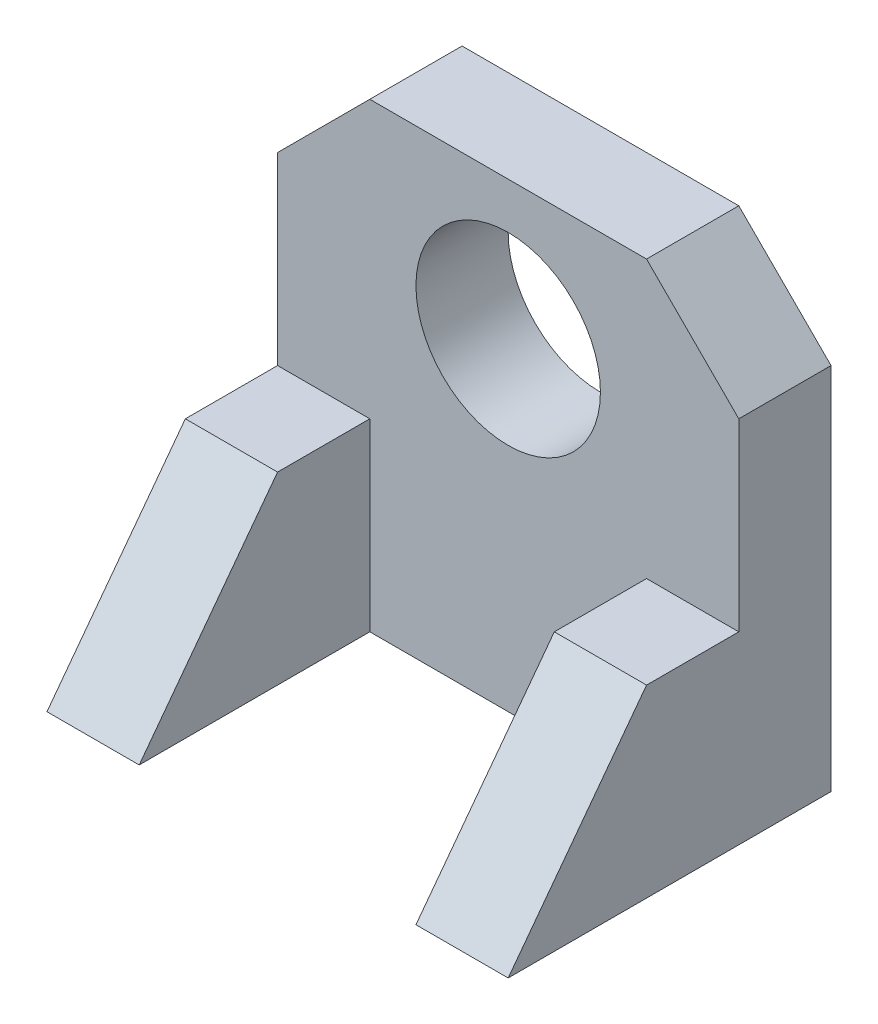
SolidWorks part; units mm, degrees
ref_plane "Front Plane" through (0, 0, 0) normal (0, 0, 1) x (1, 0, 0)
ref_plane "Top Plane" through (0, 0, 0) normal (0, 1, 0) x (1, 0, 0)
ref_plane "Right Plane" through (0, 0, 0) normal (1, 0, 0) x (0, 0, -1)
sketch "Sketch1" plane through (0, 0, 0) normal (0, 0, 1) x (1, 0, 0)
  line L1 (-15.7517, 35.0566) -> (14.2483, 35.0566)
  line L2 (-25.7517, 25.0566) -> (-25.7517, -14.9434)
  line L3 (-25.7517, -14.9434) -> (24.2483, -14.9434)
  line L4 (24.2483, 25.0566) -> (24.2483, -14.9434)
  line L5 (-15.7517, 35.0566) -> (-25.7517, 25.0566)
  line L8 (14.2483, 35.0566) -> (24.2483, 25.0566)
  dimension "D1" = 50
extrude "Boss-Extrude1" add sketch "Sketch1" against normal blind 10
sketch "Sketch2" plane through (0, 0, 0) normal (0, 0, 1) x (1, 0, 0)
  circle A0 centre (-0.7517, 20.0566) radius 10
extrude "Cut-Extrude1" cut sketch "Sketch2" against normal blind 10
sketch "Sketch3" plane through (24.2483, 0, 0) normal (1, 0, 0) x (0, 0, -1)
  line L0 (0, -14.9434) -> (-25, -14.9434)
  line L2 (0, -14.9434) -> (0, 25.0566) construction
  line L3 (0, 5.0566) -> (0, -14.9434)
  line L4 (0, 5.0566) -> (-10, 5.0566)
  line L5 (-10, 5.0566) -> (-25, -14.9434)
  dimension "D1" = 25
  dimension "D2" = 10
  dimension "D3" = 20
extrude "Boss-Extrude2" add sketch "Sketch3" against normal blind 10
sketch "Sketch4" plane through (-25.7517, 0, 0) normal (-1, 0, 0) x (0, 0, 1)
  line L0 (0, -14.9434) -> (25, -14.9434)
  line L1 (25, -14.9434) -> (10, 5.0566)
  line L2 (10, 5.0566) -> (0, 5.0566)
  line L3 (0, 25.0566) -> (0, -14.9434) construction
  line L4 (0, 5.0566) -> (0, -14.9434)
extrude "Boss-Extrude3" add sketch "Sketch4" against normal blind 10
